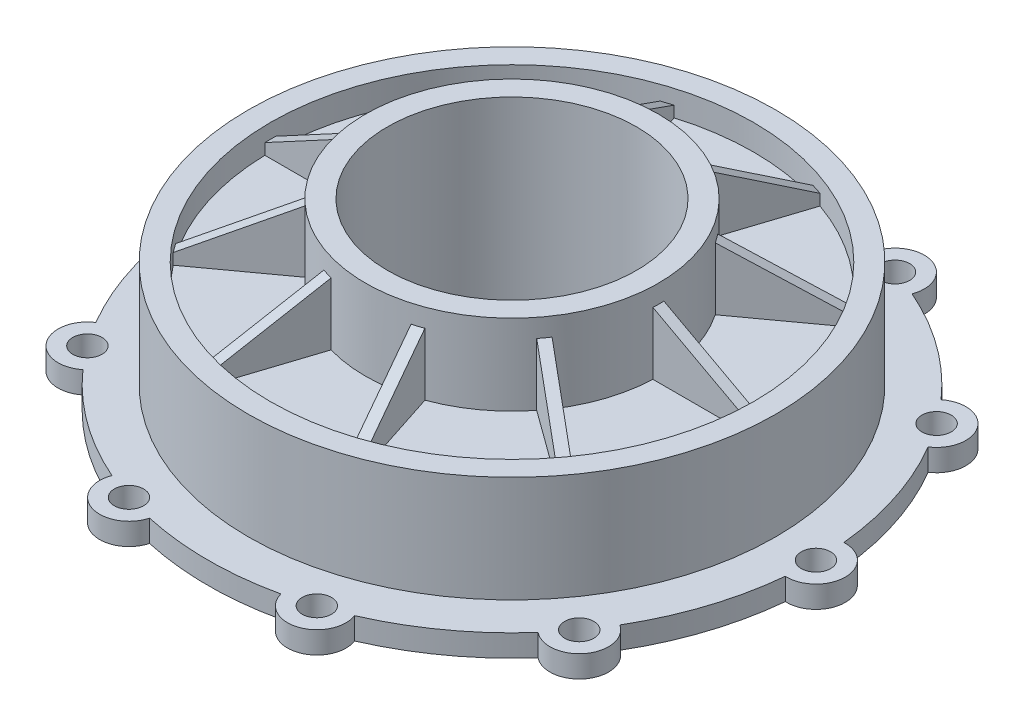
SolidWorks part; units mm, degrees
material "Alloy Steel"
ref_plane "Front Plane" through (0, 0, 0) normal (0, 0, 1) x (1, 0, 0)
ref_plane "Top Plane" through (0, 0, 0) normal (0, 1, 0) x (1, 0, 0)
ref_plane "Right Plane" through (0, 0, 0) normal (1, 0, 0) x (0, 0, -1)
sketch "Sketch1" plane through (0, 0, 0) normal (0, 0, 1) x (1, 0, 0)
  line L0 (0, 0) -> (0, 38.25) construction
  line L1 (34, 0) -> (34, 50)
  line L2 (34, 50) -> (40, 50)
  line L3 (40, 50) -> (40, 28)
  line L4 (40, 28) -> (66, 28)
  line L5 (66, 28) -> (66, 35)
  line L6 (66, 35) -> (72, 35)
  line L7 (72, 35) -> (72, 6)
  line L8 (83, 0) -> (66, 0)
  line L9 (66, 0) -> (66, 22)
  line L10 (66, 22) -> (40, 22)
  line L11 (40, 22) -> (40, 0)
  line L12 (40, 0) -> (34, 0)
  line L13 (0, 0) -> (87.3906, 0) construction
  line L14 (72, 6) -> (83, 6)
  line L15 (83, 6) -> (83, 0)
  dimension "D1" = 68
  dimension "D2" = 80
  dimension "D3" = 132
  dimension "D4" = 144
  dimension "D5" = 50
  dimension "D6" = 6
  dimension "D7" = 22
  dimension "D8" = 166
  dimension "D9" = 6
  dimension "D10" = 35
revolve "Revolve1" add sketch "Sketch1" angle 360 about L0
sketch "Sketch3" plane through (0, 6, 0) normal (0, 1, 0) x (1, 0, 0)
  circle A0 centre (-83, 0) radius 8
  circle A1 centre (0, 0) radius 83 construction
  dimension "D1" = 16
extrude "Boss-Extrude1" add sketch "Sketch3" against normal up to surface (6 mm away) up to face at (0, 0, -83)
sketch "Sketch4" plane through (0, 6, 0) normal (0, 1, 0) x (1, 0, 0)
  circle A0 centre (-83, 0) radius 4
  dimension "D1" = 8
extrude "Cut-Extrude1" cut sketch "Sketch4" against normal through all
pattern_circular "CirPattern2" count 10 over 360 about axis through (0, 0, 0) along (0, 1, 0) of "Cut-Extrude1", "Boss-Extrude1"
sketch "Sketch2" plane through (0, 0, 0) normal (0, 0, 1) x (1, 0, 0)
  line L0 (-40, 45) -> (-66, 31)
  line L1 (-40, 50) -> (-40, 28) construction
  line L2 (-66, 35) -> (-66, 28) construction
  line L5 (66, 28) -> (-66, 28) construction
  line L6 (72, 35) -> (-72, 35) construction
  dimension "D1" = 3
  dimension "D2" = 10
rib "Rib1" sketch "Sketch2" sketch "Sketch2" thickness 3 extrusion direction parallel to sketch draft on no parameters "D1"=3
pattern_circular "CirPattern1" count 10 over 360 about axis through (0, 0, 0) along (0, 1, 0) of "Rib1"
sketch "Sketch5" plane through (0, 0, 0) normal (0, -1, 0) x (1, 0, 0)
  line L0 (0, 0) -> (-110.0838, 0) construction
  line L1 (-40, 0) -> (-66, 0)
  circle A0 centre (0, 0) radius 40 construction
  circle A1 centre (0, 0) radius 66 construction
rib "Rib2" sketch "Sketch5" sketch "Sketch5" thickness 3 extrusion direction normal to sketch draft on no parameters "D1"=3
pattern_circular "CirPattern3" count 10 over 360 about axis through (0, 0, 0) along (0, -1, 0) of "Rib2"
